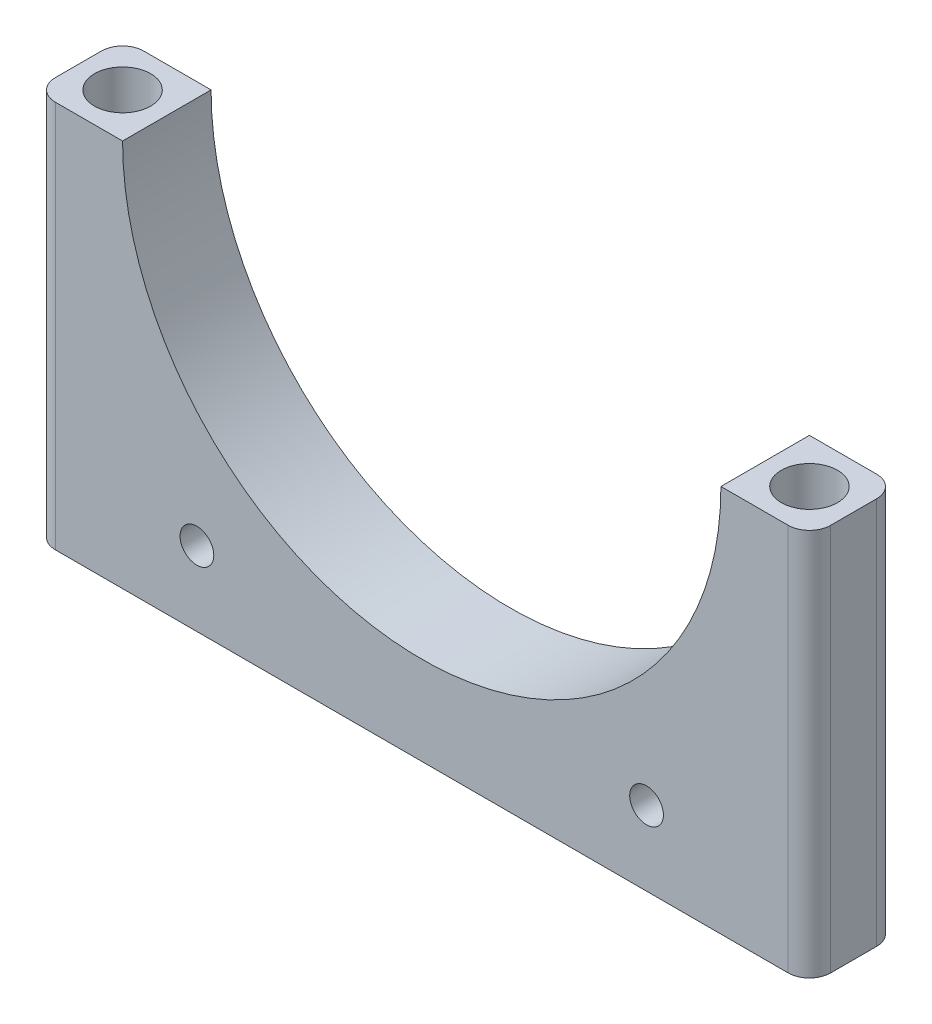
SolidWorks part; units mm, degrees
ref_plane "Front Plane" through (0, 0, 0) normal (0, 0, 1) x (1, 0, 0)
ref_plane "Top Plane" through (0, 0, 0) normal (0, 1, 0) x (1, 0, 0)
ref_plane "Right Plane" through (0, 0, 0) normal (1, 0, 0) x (0, 0, -1)
sketch "Sketch4" plane through (0, 0, 0) normal (0, 0, 1) x (1, 0, 0)
  line L0 (0, 0) -> (0, 169)
  line L1 (-84.5, 84.5) -> (84.5, 84.5)
  line L2 (0, 0) -> (0, 194)
  line L3 (-109.5, 84.5) -> (-109.5, -25)
  line L4 (109.5, 84.5) -> (109.5, -25)
  line L5 (109.5, -25) -> (0, -25)
  line L6 (0, -25) -> (-109.5, -25)
  line L7 (-109.5, 84.5) -> (109.5, 84.5)
  circle A0 centre (0, 84.5) radius 84.5
  circle A1 centre (0, 84.5) radius 109.5
  dimension "D1" = 169
  dimension "D2" = 25
extrude "Boss-Extrude1" add sketch "Sketch4" along normal blind 25 contours A1 L3 L6 | L7 A1 A0 | A1 L5 L4
sketch "Sketch5" plane through (0, 84.5, 0) normal (0, 1, 0) x (1, 0, 0)
  line L0 (0, 0) -> (0, -33.3515) construction
  line L1 (-109.5, 0) -> (-84.5, 0) construction
  line L2 (-109.5, -25) -> (-109.5, 0) construction
  circle A0 centre (-97, -12.5) radius 7.94
  circle A1 centre (97, -12.5) radius 7.94
  dimension "D1" = 15.88
  dimension "D2" = 12.5
  dimension "D3" = 12.5
extrude "Cut-Extrude1" cut sketch "Sketch5" against normal blind 5000 contours A0 | A1
sketch "Sketch6" plane through (0, 0, 25) normal (0, 0, 1) x (1, 0, 0)
  line L0 (-84.5, 84.5) -> (-84.5, -25)
  line L1 (109.5, -25) -> (-109.5, -25) construction
  line L2 (-63.5, 28.7506) -> (-63.5, -4)
  line L3 (0, 0) -> (0, -39.0782) construction
  arc A0 (-84.5, 84.5) -> (84.5, 84.5) centre (0, 84.5) ccw construction
  circle A1 centre (-63.5, -4) radius 4.7625
  circle A2 centre (63.5, -4) radius 4.7625
  dimension "D1" = 9.525
  dimension "D2" = 21
  dimension "D3" = 21
extrude "Cut-Extrude2" cut sketch "Sketch6" against normal blind 5000
fillet "Fillet2" radius 6 4 edges at (109.5, 29.75, 25) (109.5, 29.75, 0) (-109.5, 29.75, 25) (-109.5, 29.75, 0)
